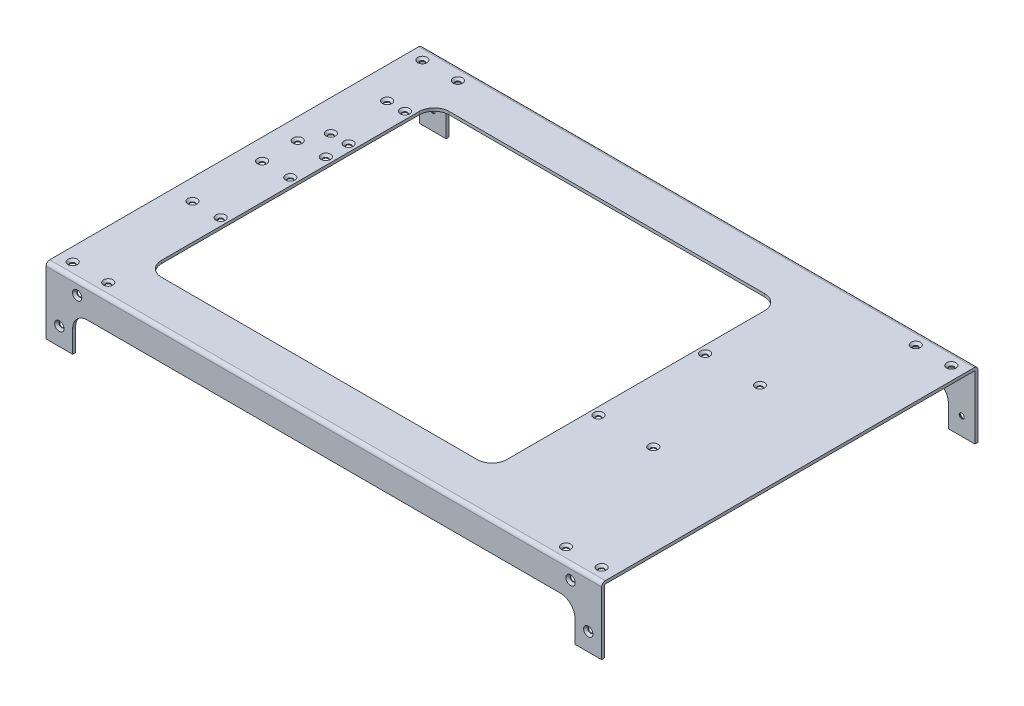
SolidWorks part; units mm, degrees
material "6061-T6 (SS)"
ref_plane "Front Plane" through (0, 0, 0) normal (0, 0, 1) x (1, 0, 0)
ref_plane "Top Plane" through (0, 0, 0) normal (0, 1, 0) x (1, 0, 0)
ref_plane "Right Plane" through (0, 0, 0) normal (1, 0, 0) x (0, 0, -1)
sketch "Sketch1" plane through (0, 0, 0) normal (1, 0, 0) x (0, 0, -1)
  line L0 (125, -45) -> (127, -45)
  line L1 (-124.5, 0) -> (124.5, 0)
  line L2 (-127, -2.5) -> (-127, -45)
  line L3 (-127, -45) -> (-125, -45)
  line L4 (127, -2.5) -> (127, -45)
  line L6 (-125, -45) -> (-125, -2.5)
  line L7 (-124.5, -2) -> (124.5, -2)
  line L8 (125, -45) -> (125, -2.5)
  arc A0 (-124.5, 0) -> (-127, -2.5) centre (-124.5, -2.5) ccw
  arc A1 (124.5, 0) -> (127, -2.5) centre (124.5, -2.5) cw
  arc A2 (124.5, -2) -> (125, -2.5) centre (124.5, -2.5) cw
  arc A3 (-125, -2.5) -> (-124.5, -2) centre (-124.5, -2.5) cw
  dimension "D1" = 2.5
  dimension "D2" = 250
  dimension "D3" = 2
  dimension "D4" = 45
extrude "Boss-Extrude1" add sketch "Sketch1" along normal mid plane 375
sketch "Sketch2" plane through (0, 0, 127) normal (0, 0, 1) x (1, 0, 0)
  line L0 (187.5, -45) -> (-187.5, -45) construction
  line L1 (-169.5, -45) -> (169.5, -45)
  line L2 (-169.5, -45) -> (-169.5, -30)
  line L3 (-159.5, -20) -> (159.5, -20)
  line L4 (169.5, -45) -> (169.5, -30)
  line L5 (-187.5, -2.5) -> (-187.5, -45) construction
  line L6 (187.5, 0) -> (-187.5, 0) construction
  line L7 (187.5, -2.5) -> (187.5, -45) construction
  arc A0 (159.5, -20) -> (169.5, -30) centre (159.5, -30) cw
  arc A1 (-169.5, -30) -> (-159.5, -20) centre (-159.5, -30) cw
  dimension "D4" = 10
  dimension "D1" = 18
  dimension "D2" = 20
  dimension "D3" = 18
extrude "Cut-Extrude1" cut sketch "Sketch2" against normal through all
sketch "Sketch3" plane through (0, 0, 0) normal (0, 1, 0) x (1, 0, 0)
  line L1 (-139.5, 97) -> (73.5, 97)
  line L2 (-149.5, 87) -> (-149.5, -87)
  line L3 (-139.5, -97) -> (73.5, -97)
  line L4 (83.5, 87) -> (83.5, -87)
  line L6 (187.5, 127) -> (-187.5, 127) construction
  line L7 (187.5, -127) -> (-187.5, -127) construction
  line L8 (187.5, 124.5) -> (187.5, -124.5) construction
  line L9 (-187.5, 124.5) -> (-187.5, -124.5) construction
  arc A0 (-149.5, -87) -> (-139.5, -97) centre (-139.5, -87) ccw
  arc A1 (73.5, -97) -> (83.5, -87) centre (73.5, -87) ccw
  arc A2 (83.5, 87) -> (73.5, 97) centre (73.5, 87) ccw
  arc A3 (-139.5, 97) -> (-149.5, 87) centre (-139.5, 87) ccw
  dimension "D5" = 10
  dimension "D1" = 30
  dimension "D2" = 30
  dimension "D3" = 104
  dimension "D4" = 38
extrude "Cut-Extrude2" cut sketch "Sketch3" against normal blind 10
sketch "Sketch4" plane through (0, 0, 127) normal (0, 0, 1) x (1, 0, 0)
  line L0 (-187.5, -2.5) -> (-187.5, -45) construction
  line L1 (187.5, 0) -> (-187.5, 0) construction
  line L2 (187.5, -2.5) -> (187.5, -45) construction
  circle A0 centre (-178.5, -33) radius 1.5
  circle A1 centre (-178.5, -9) radius 1.5 construction
  circle A2 centre (-166.5, -9) radius 1.5
  circle A3 centre (166.5, -9) radius 1.5
  circle A4 centre (178.5, -9) radius 1.5 construction
  circle A5 centre (178.5, -33) radius 1.5
  dimension "D1" = 3
  dimension "D2" = 9
  dimension "D3" = 9
  dimension "D4" = 9
  dimension "D5" = 21
  dimension "D6" = 33
  dimension "D7" = 21
extrude "Cut-Extrude3" cut sketch "Sketch4" against normal through all
sketch "Sketch5" plane through (0, 0, 0) normal (0, 1, 0) x (1, 0, 0)
  line L0 (187.5, 127) -> (-187.5, 127) construction
  line L1 (187.5, -127) -> (-187.5, -127) construction
  line L2 (-187.5, 124.5) -> (-187.5, -124.5) construction
  line L3 (187.5, 124.5) -> (187.5, -124.5) construction
  circle A0 centre (-178.5, 118) radius 1.5
  circle A1 centre (-154.5, 118) radius 1.5
  circle A2 centre (154.5, 118) radius 1.5
  circle A3 centre (178.5, 118) radius 1.5
  circle A4 centre (178.5, -118) radius 1.5
  circle A5 centre (154.5, -118) radius 1.5
  circle A6 centre (-178.5, -118) radius 1.5
  circle A7 centre (-154.5, -118) radius 1.5
  circle A8 centre (88.5, 41.85) radius 1.5
  circle A9 centre (88.5, -30.15) radius 1.5
  circle A10 centre (125.5, 41.85) radius 1.5
  circle A11 centre (125.5, -30.15) radius 1.5
  circle A12 centre (-154.5, 28.85) radius 1.5
  circle A13 centre (-173.5, 28.85) radius 1.5
  circle A14 centre (-173.5, 4.85) radius 1.5
  circle A15 centre (-154.5, 4.85) radius 1.5
  circle A16 centre (-154.5, -42.15) radius 1.5
  circle A17 centre (-173.5, -42.15) radius 1.5
  circle A18 centre (-166.5, 82.25) radius 1.5
  circle A19 centre (-154.5, 82.25) radius 1.5
  circle A20 centre (-166.5, 44.25) radius 1.5
  circle A21 centre (-154.5, 44.25) radius 1.5
  dimension "D1" = 3
  dimension "D2" = 9
  dimension "D3" = 9
  dimension "D4" = 9
  dimension "D5" = 33
  dimension "D6" = 9
  dimension "D7" = 33
extrude "Cut-Extrude4" cut sketch "Sketch5" against normal blind 10
hole_wizard "CSK for M3 Flat Head Machine Screw1" positions "Sketch7" profile "Sketch6" countersink size "M3" standard "Ansi Metric" end condition through all
sketch "Sketch7" plane through (0, 0, 0) normal (0, 1, 0) x (-1, 0, 0)
  point P0 (154.5, 118)
  point P1 (178.5, 118)
  point P7 (154.5, 42.15)
  point P10 (173.5, 42.15)
  point P13 (154.5, -4.85)
  point P16 (173.5, -4.85)
  point P19 (173.5, -28.85)
  point P22 (154.5, -28.85)
  point P25 (154.5, -44.25)
  point P28 (166.5, -44.25)
  point P31 (166.5, -82.25)
  point P34 (154.5, -82.25)
  point P37 (178.5, -118)
  point P40 (154.5, -118)
  point P43 (-154.5, -118)
  point P46 (-178.5, -118)
  point P49 (-125.5, -41.85)
  point P52 (-88.5, -41.85)
  point P55 (-125.5, 30.15)
  point P58 (-88.5, 30.15)
  point P61 (-178.5, 118)
  point P64 (-154.5, 118)
sketch "Sketch6" plane through (-154.5, 0, 118) normal (1, 0, 0) x (0, 0, 1)
  line L0 (0, 0) -> (0, 45)
  line L1 (0, 45) -> (1.7, 45)
  line L2 (1.7, 45) -> (1.7, 1.45)
  line L3 (1.7, 1.45) -> (3.15, 0)
  line L5 (3.15, 0) -> (0, 0)
  line L6 (-1.7, 1.45) -> (-3.15, 0) construction
  line L11 (0, -6.35) -> (0, 107.95) construction
  dimension "Thru Hole Dia." = 3.4
  dimension "Thru Hole Depth" = 45
  dimension "Near C'Sink Dia." = 6.3
  dimension "Near C'Sink Angle" = 90
hole_wizard "CSK for M3 Flat Head Machine Screw2" positions "Sketch9" profile "Sketch8" countersink size "M3" standard "Ansi Metric"
sketch "Sketch9" plane through (0, 0, 127) normal (0, 0, 1) x (1, 0, 0)
  point P0 (166.5, -9)
  point P1 (178.5, -33)
  point P4 (-178.5, -33)
  point P7 (-166.5, -9)
sketch "Sketch8" plane through (166.5, -9, 127) normal (1, 0, 0) x (0, -1, 0)
  line L0 (0, 0) -> (0, 11.0215)
  line L1 (0, 11.0215) -> (1.7, 10)
  line L2 (1.7, 10) -> (1.7, 1.45)
  line L3 (1.7, 1.45) -> (3.15, 0)
  line L5 (3.15, 0) -> (0, 0)
  line L6 (-1.7, 1.45) -> (-3.15, 0) construction
  line L10 (0, 11.0215) -> (-1.7, 10) construction
  line L11 (0, -6.35) -> (0, 107.95) construction
  dimension "Hole Dia." = 3.4
  dimension "Hole Depth" = 10
  dimension "Near C'Sink Dia." = 6.3
  dimension "Near C'Sink Angle" = 90
  dimension "Drill Angle" = 118
hole_wizard "CSK for M3 Flat Head Machine Screw3" positions "Sketch11" profile "Sketch10" countersink size "M3" standard "Ansi Metric"
sketch "Sketch11" plane through (0, 0, -127) normal (0, 0, -1) x (-1, 0, 0)
  point P0 (-166.5, -9)
  point P1 (178.5, -33)
  point P4 (166.5, -9)
  point P7 (-178.5, -33)
sketch "Sketch10" plane through (166.5, -9, -127) normal (1, 0, 0) x (0, 1, 0)
  line L0 (0, 0) -> (0, 11.0215)
  line L1 (0, 11.0215) -> (1.7, 10)
  line L2 (1.7, 10) -> (1.7, 1.45)
  line L3 (1.7, 1.45) -> (3.15, 0)
  line L5 (3.15, 0) -> (0, 0)
  line L6 (-1.7, 1.45) -> (-3.15, 0) construction
  line L10 (0, 11.0215) -> (-1.7, 10) construction
  line L11 (0, -6.35) -> (0, 107.95) construction
  dimension "Hole Dia." = 3.4
  dimension "Hole Depth" = 10
  dimension "Near C'Sink Dia." = 6.3
  dimension "Near C'Sink Angle" = 90
  dimension "Drill Angle" = 118
